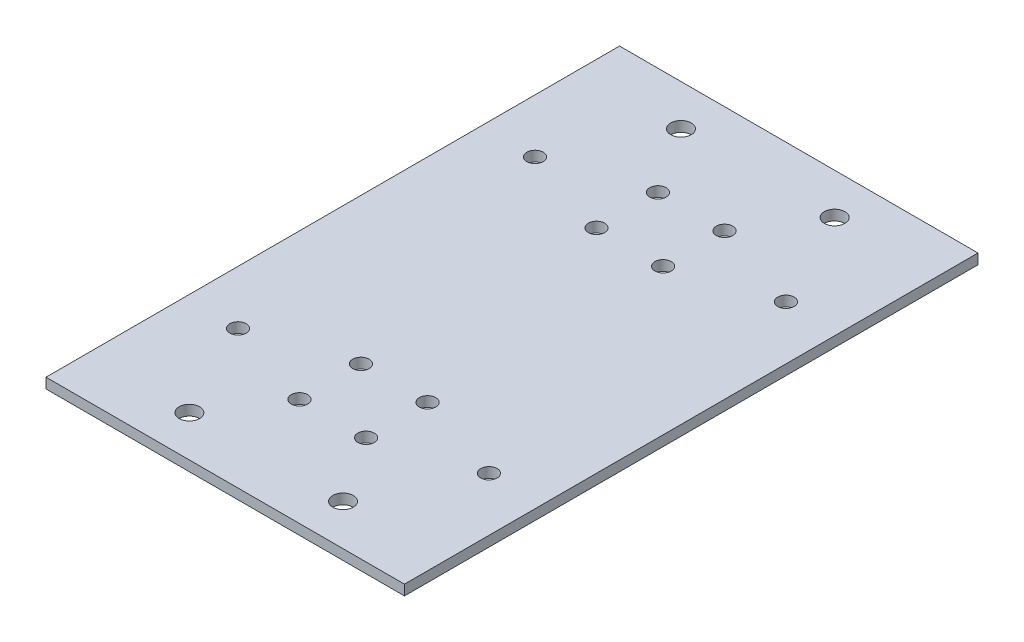
SolidWorks part; units mm, degrees
ref_plane "前基準面" through (0, 0, 0) normal (0, 0, 1) x (1, 0, 0)
ref_plane "上基準面" through (0, 0, 0) normal (0, 1, 0) x (1, 0, 0)
ref_plane "右基準面" through (0, 0, 0) normal (1, 0, 0) x (0, 0, -1)
sketch "草圖2" plane through (0, 0, 0) normal (0, 1, 0) x (1, 0, 0)
  line L1 (-35, -56) -> (35, -56)
  line L2 (-35, -56) -> (-35, 56)
  line L3 (-35, 56) -> (35, 56)
  line L4 (35, -56) -> (35, 56)
  line L5 (0, 56) -> (0, -56) construction
  line L6 (-35, 0) -> (35, 0) construction
  circle A0 centre (-6.5, 35) radius 1.6
  circle A1 centre (-6.5, -35) radius 1.6
  circle A2 centre (-6.5, 23) radius 1.6
  circle A3 centre (-6.5, -23) radius 1.6
  circle A4 centre (6.5, -35) radius 1.6
  circle A5 centre (6.5, -23) radius 1.6
  circle A6 centre (6.5, 23) radius 1.6
  circle A7 centre (6.5, 35) radius 1.6
  circle A8 centre (-24.5, 29) radius 1.6
  circle A9 centre (24.5, 29) radius 1.6
  circle A10 centre (-24.5, -29) radius 1.6
  circle A11 centre (24.5, -29) radius 1.6
  point P0 (0, 0)
  dimension "D4" = 3.2
  dimension "D9" = 3.2
  dimension "D1" = 112
  dimension "D2" = 70
  dimension "D3" = 58
  dimension "D5" = 13
  dimension "D6" = 12
  dimension "D7" = 58
  dimension "D8" = 49
extrude "填料-伸長1" add sketch "草圖2" along normal blind 2
sketch "草圖3" plane through (0, 2, 0) normal (0, 1, 0) x (1, 0, 0)
  line L0 (0, -75.2857) -> (0, 75.2857) construction
  line L1 (-75.5857, 0) -> (75.5857, 0) construction
  line L2 (-35, -56) -> (35, -56) construction
  circle A0 centre (-15, -48) radius 2
  circle A1 centre (-15, 48) radius 2
  circle A2 centre (15, -48) radius 2
  circle A3 centre (15, 48) radius 2
  point P4 (0, 0)
  point P7 (0, 0)
  dimension "D2" = 4
  dimension "D1" = 30
  dimension "D3" = 8
extrude "除料-伸長1" cut sketch "草圖3" against normal through all
